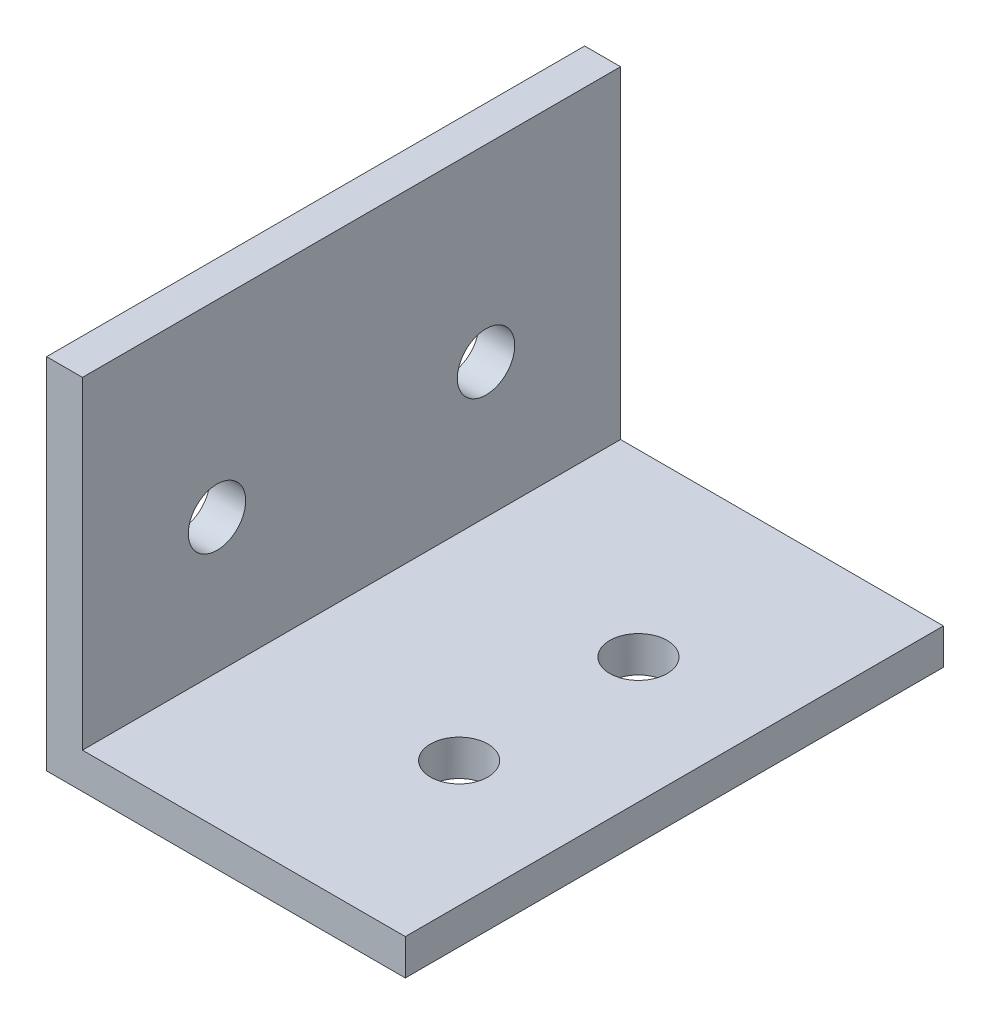
SolidWorks part; units mm, degrees
ref_plane "Front Plane" through (0, 0, 0) normal (0, 0, 1) x (1, 0, 0)
ref_plane "Top Plane" through (0, 0, 0) normal (0, 1, 0) x (1, 0, 0)
ref_plane "Right Plane" through (0, 0, 0) normal (1, 0, 0) x (0, 0, -1)
sketch "Sketch1" plane through (0, 0, 0) normal (0, 0, 1) x (1, 0, 0)
  line L0 (0, 20) -> (0, 0)
  line L1 (0, 0) -> (20, 0)
  line L2 (2, 20) -> (2, 2)
  line L3 (2, 2) -> (20, 2)
  line L4 (0, 20) -> (2, 20)
  line L5 (20, 2) -> (20, 0)
  dimension "D1" = 20
  dimension "D2" = 20
  dimension "D3" = 2
extrude "Boss-Extrude1" add sketch "Sketch1" along normal blind 30
sketch "Sketch2" plane through (0, 0, 0) normal (1, 0, 0) x (0, 0, -1)
  line L0 (-30, 2) -> (-30, 20) construction
  line L1 (-30, 2) -> (0, 2) construction
  line L2 (0, 2) -> (0, 20) construction
  circle A0 centre (-22.5, 9.5) radius 1.6
  circle A1 centre (-7.5, 9.5) radius 1.6
  point P4 (0, 0)
  dimension "D1" = 3.2
  dimension "D2" = 3.2
  dimension "D3" = 7.5
  dimension "D4" = 7.5
  dimension "D5" = 7.5
  dimension "D6" = 7.5
extrude "Cut-Extrude1" cut sketch "Sketch2" along normal blind 10
sketch "Sketch3" plane through (0, 0, 0) normal (0, 1, 0) x (1, 0, 0)
  line L0 (20, -30) -> (2, -30) construction
  line L1 (20, 0) -> (2, 0) construction
  line L2 (20, -30) -> (20, 0) construction
  circle A0 centre (13, -10) radius 1.6
  circle A1 centre (13, -20) radius 1.6
  dimension "D1" = 3.2
  dimension "D2" = 3.2
  dimension "D3" = 10
  dimension "D4" = 10
  dimension "D5" = 7
  dimension "D6" = 7
extrude "Cut-Extrude2" cut sketch "Sketch3" along normal blind 4
